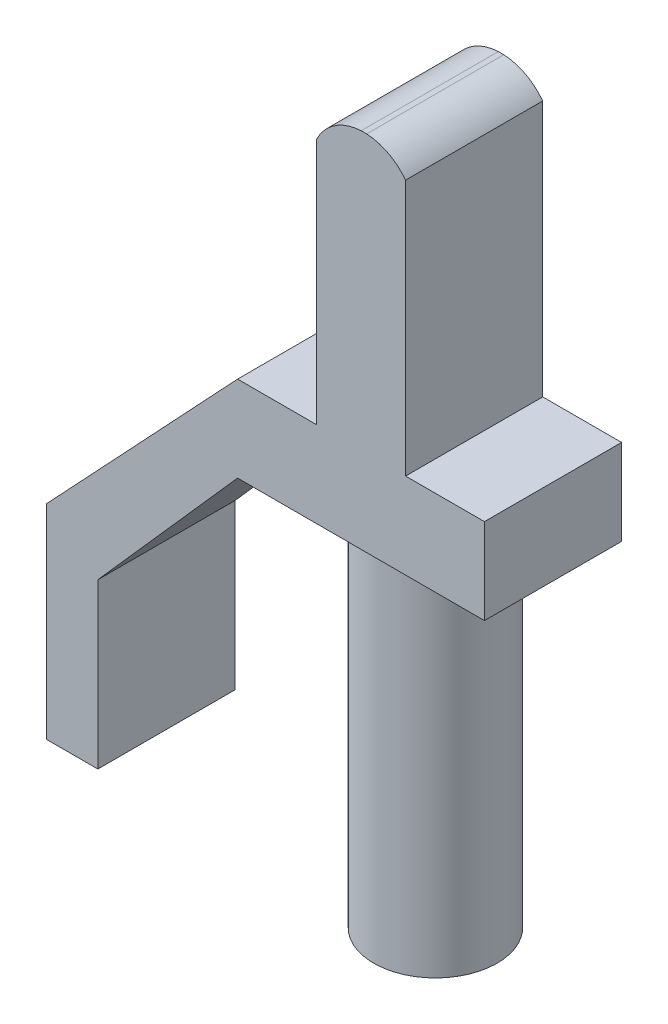
SolidWorks part; units mm, degrees
material "ПК/АБС"
ref_plane "Front Plane" through (0, 0, 0) normal (0, 0, 1) x (1, 0, 0)
ref_plane "Top Plane" through (0, 0, 0) normal (0, 1, 0) x (1, 0, 0)
ref_plane "Right Plane" through (0, 0, 0) normal (1, 0, 0) x (0, 0, -1)
sketch "Sketch1" plane through (0, 0, 0) normal (0, 0, 1) x (1, 0, 0)
  line L0 (-10.4087, 3.5764) -> (-7.8087, 3.5764)
  line L1 (-9.1087, 9.2687) -> (-9.1087, 10.4552) construction
  line L2 (-10.4087, 3.5764) -> (-10.4087, 10.7764)
  line L3 (-7.8087, 3.5764) -> (-7.8087, 11.055)
  line L4 (-9.1039, 11.6552) -> (-8.9448, 11.6552)
  arc A0 (-10.4087, 10.7764) -> (-9.1039, 11.6552) centre (-9.0244, 10.129) cw
  arc A1 (-8.9448, 11.6552) -> (-7.8087, 11.055) centre (-9.0244, 10.129) cw
  point P8 (-9.1087, 3.5764)
  dimension "D1" = 1.5282
  dimension "D2" = 7.2
  dimension "D3" = 2.6
extrude "Boss-Extrude1" add sketch "Sketch1" along normal blind 4
sketch "Эскиз1" plane through (0, 0, 4) normal (0, 0, 1) x (1, 0, 0)
  line L1 (-12.7087, 3.58) -> (-5.5087, 3.58)
  line L2 (-12.7087, 3.58) -> (-12.7087, 1.08)
  line L3 (-12.7087, 1.08) -> (-5.5087, 1.08)
  line L4 (-5.5087, 3.58) -> (-5.5087, 1.08)
  dimension "D1" = 2.3
  dimension "D2" = 2.3
  dimension "D3" = 2.5
extrude "Бобышка-Вытянуть1" add sketch "Эскиз1" against normal blind 4
sketch "Эскиз5" plane through (0, 0, 4) normal (0, 0, 1) x (1, 0, 0)
  line L0 (-12.7087, 3.58) -> (-18.2841, -2.3575)
  line L1 (-18.2841, -2.3575) -> (-18.2841, -8.3075)
  line L2 (-18.2841, -11.7305) -> (-18.2841, -7.5305) construction
  line L3 (-18.2841, -8.3075) -> (-16.7841, -8.3075)
  line L4 (-16.7841, -8.3075) -> (-16.7841, -3.525)
  line L5 (-12.7087, 1.08) -> (-16.7841, -3.525)
  line L14 (-10.4087, 10.7764) -> (-10.4087, 3.58)
  line L15 (-10.4087, 3.58) -> (-12.7087, 3.58)
  line L16 (-12.7087, 3.58) -> (-12.7087, 1.08)
  line L17 (-12.7087, 1.08) -> (-5.5087, 1.08)
  line L18 (-5.5087, 1.08) -> (-5.5087, 3.58)
  line L19 (-5.5087, 3.58) -> (-7.8087, 3.58)
  line L20 (-7.8087, 3.58) -> (-7.8087, 11.055)
  line L21 (-8.9448, 11.6552) -> (-9.1039, 11.6552)
  line L24 (-12.7087, 3.58) -> (-12.7087, 1.08)
  arc A2 (-7.8087, 11.055) -> (-8.9448, 11.6552) centre (-9.0244, 10.129) ccw
  arc A3 (-9.1039, 11.6552) -> (-10.4087, 10.7764) centre (-9.0244, 10.129) ccw
  dimension "D1" = 5.95
  dimension "D4" = 1.5
  dimension "D2" = 0
extrude "Бобышка-Вытянуть2" add sketch "Эскиз5" against normal up to vertex (4 mm away)
sketch "Эскиз6" plane through (0, 1.08, 0) normal (0, -1, 0) x (1, 0, 0)
  line L7 (-12.7087, 4) -> (-5.5087, 4) construction
  line L8 (-12.7087, 1.6) -> (-5.5087, 1.6) construction
  line L9 (-12.7087, 0) -> (-12.7087, 4) construction
  line L10 (-5.5087, 0) -> (-5.5087, 4) construction
  circle A0 centre (-9.1184, 1.82) radius 1.8
  dimension "D1" = 2.18
extrude "Бобышка-Вытянуть3" add sketch "Эскиз6" along normal blind 10.65
